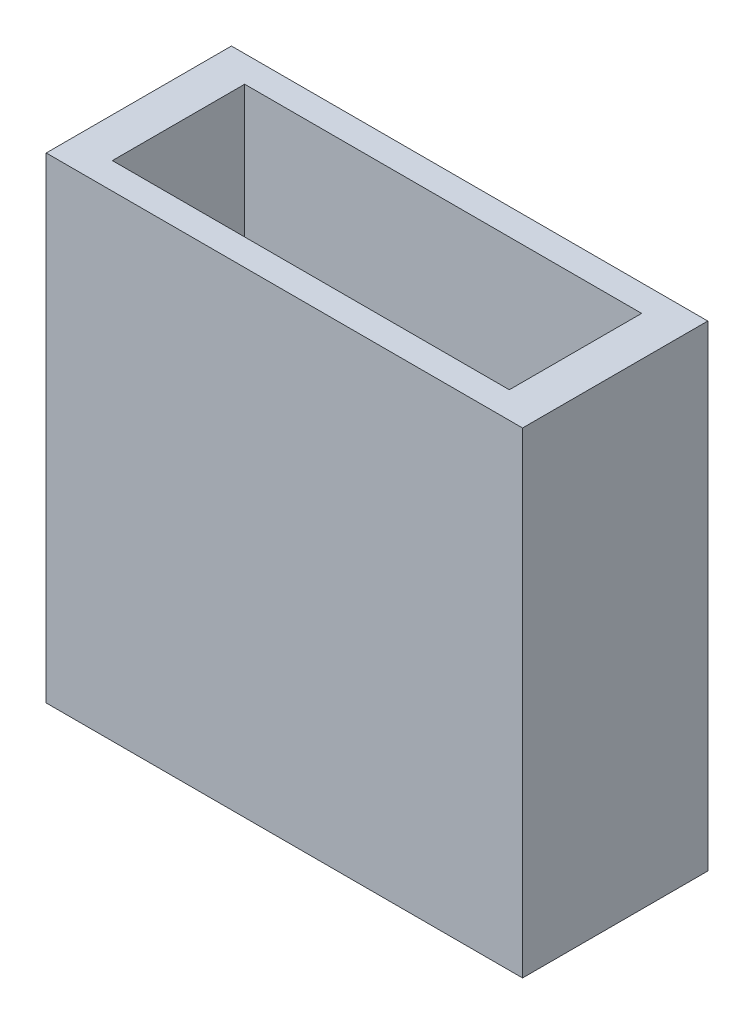
SolidWorks part; units mm, degrees
ref_plane "Front Plane" through (0, 0, 0) normal (0, 0, 1) x (1, 0, 0)
ref_plane "Top Plane" through (0, 0, 0) normal (0, 1, 0) x (1, 0, 0)
ref_plane "Right Plane" through (0, 0, 0) normal (1, 0, 0) x (0, 0, -1)
sketch "Sketch1" plane through (0, 0, 0) normal (0, 1, 0) x (1, 0, 0)
  line L1 (0, 0) -> (45.72, 0)
  line L2 (0, 0) -> (0, 17.78)
  line L3 (0, 17.78) -> (45.72, 17.78)
  line L4 (45.72, 0) -> (45.72, 17.78)
  dimension "D1" = 45.72
  dimension "D2" = 17.78
extrude "Boss-Extrude1" add sketch "Sketch1" along normal blind 45.72
ref_plane "Plane1" through (0, 45.72, 0) normal (0, 1, 0) x (1, 0, 0)
sketch "Sketch2" plane through (0, 45.72, 0) normal (0, 1, 0) x (1, 0, 0)
  line L0 (0, 17.78) -> (0, 0) construction
  line L1 (3.81, 2.54) -> (41.91, 2.54)
  line L2 (3.81, 2.54) -> (3.81, 15.24)
  line L3 (3.81, 15.24) -> (41.91, 15.24)
  line L4 (41.91, 2.54) -> (41.91, 15.24)
  line L5 (45.72, 0) -> (45.72, 17.78) construction
  line L6 (0, 0) -> (45.72, 0) construction
  line L7 (45.72, 17.78) -> (0, 17.78) construction
  dimension "D1" = 3.81
  dimension "D2" = 3.81
  dimension "D3" = 2.54
  dimension "D4" = 2.54
extrude "Cut-Extrude1" cut sketch "Sketch2" against normal blind 41.91
sketch "Sketch4" plane through (0, 0, 0) normal (0, 0, 1) x (1, 0, 0)
  line L0 (0, 0) -> (25.4, 4.7076)
  line L1 (0, 0) -> (45.72, 0) construction
  dimension "D1" = 10.5
  dimension "D2" = 25.4
sketch "Sketch5" plane through (0, 0, 0) normal (0, 1, 0) x (1, 0, 0)
  line L0 (0, 0) -> (3.9734, 25.0873)
  line L1 (0, 0) -> (25.4, 0) construction
  dimension "D1" = 81
  dimension "D2" = 25.4
ref_plane "Plane3" through (0, 0, 0) normal (0.1822, -0.9828, 0.0289) x (0.9745, 0.1765, -0.1385)
sketch "Sketch6" plane through (0, 0, 0) normal (0.1822, -0.9828, 0.0289) x (0.9745, 0.1765, -0.1385)
  line L0 (44.5542, 5.9899) -> (47.0164, -11.6113) construction
  line L1 (47.0164, -11.6113) -> (2.4622, -17.6012) construction
  circle A0 centre (23.1283, -5.8529) radius 3.048
  circle A1 centre (16.0797, -6.8005) radius 3.048
  circle A2 centre (30.1769, -4.9052) radius 3.048
  dimension "D2" = 6.096
  dimension "D4" = 6.096
  dimension "D5" = 6.096
  dimension "D1" = 22.86
  dimension "D3" = 8.89
  dimension "D6" = 7.112
  dimension "D7" = 7.112
  dimension "D8" = 8.89
  dimension "D9" = 8.89
extrude "Cut-Extrude2" cut sketch "Sketch6" against normal blind 15.24 and the other way through all
equation "\"x\"=0.296138"
